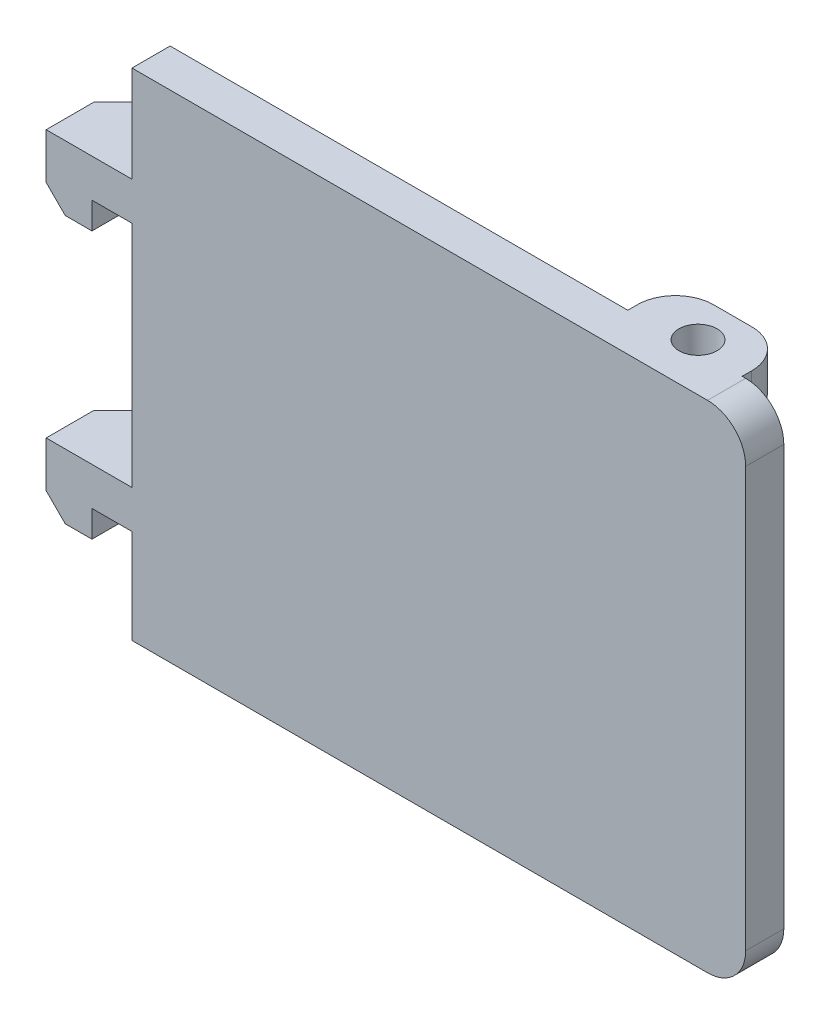
SolidWorks part; units mm, degrees
ref_plane "前视基准面" through (0, 0, 0) normal (0, 0, 1) x (1, 0, 0)
ref_plane "上视基准面" through (0, 0, 0) normal (0, 1, 0) x (1, 0, 0)
ref_plane "右视基准面" through (0, 0, 0) normal (1, 0, 0) x (0, 0, -1)
other "Configuration Table"
sketch "草图2" plane through (0, 0, 0) normal (0, 0, 1) x (1, 0, 0)
  line L1 (15.1907, -6.4342) -> (-16.9928, -6.4342)
  line L2 (15.1907, -6.4342) -> (15.1907, -32.4342)
  line L3 (15.1907, -32.4342) -> (-16.9928, -32.4342)
  line L4 (-16.9928, -6.4342) -> (-16.9928, -32.4342)
  line L6 (13.1907, -6.4342) -> (-12.8093, -6.4342) construction
  dimension "D1" = 32.1835
  dimension "D2" = 26
extrude "凸台-拉伸1" add sketch "草图2" along normal blind 2
fillet "圆角1" radius 2 2 edges at (15.1907, -32.4342, 1) (15.1907, -6.4342, 1)
sketch "草图5" plane through (0, 0, 0) normal (0, 0, -1) x (-1, 0, 0)
  line L1 (-13.0072, -6.4342) -> (-7.0072, -6.4342)
  line L2 (-13.0072, -6.4342) -> (-13.0072, -8.4342)
  line L3 (-13.0072, -8.4342) -> (-7.0072, -8.4342)
  line L4 (-7.0072, -6.4342) -> (-7.0072, -8.4342)
  line L5 (16.9928, -32.4342) -> (-13.1907, -32.4342) construction
  line L6 (-13.0072, -32.4342) -> (-7.0072, -32.4342)
  line L7 (-13.0072, -32.4342) -> (-13.0072, -30.4342)
  line L8 (-13.0072, -30.4342) -> (-7.0072, -30.4342)
  line L9 (-7.0072, -32.4342) -> (-7.0072, -30.4342)
  line L11 (16.9928, -6.4342) -> (16.9928, -32.4342) construction
  line L12 (-13.1907, -6.4342) -> (16.9928, -6.4342) construction
  dimension "D1" = 2
  dimension "D2" = 24
  dimension "D3" = 6
extrude "凸台-拉伸2" add sketch "草图5" along normal blind 2.5
fillet "圆角2" radius 2 4 edges at (7.0072, -7.4342, -2.5) (13.0072, -7.4342, -2.5) (7.0072, -31.4342, -2.5) (13.0072, -31.4342, -2.5)
sketch "草图6" plane through (0, -32.4342, 0) normal (0, -1, 0) x (1, 0, 0)
  line L1 (17.1907, 2) -> (17.1907, -8) construction
  line L2 (-16.9928, 2) -> (13.1907, 2) construction
  circle A0 centre (10.1907, -0.5) radius 1
  dimension "D1" = 2
  dimension "D2" = 7
  dimension "D3" = 2.5
extrude "切除-拉伸3" cut sketch "草图6" against normal blind 4 draft 2
sketch "草图7" plane through (0, -6.4342, 0) normal (0, 1, 0) x (1, 0, 0)
  circle A0 centre (10.1907, 0.5) radius 1
  arc A1 (10.9751, 0) -> (9.4064, 0) centre (10.1907, 0.5) ccw construction
extrude "切除-拉伸4" cut sketch "草图7" against normal blind 4 draft 2
sketch "草图8" plane through (0, 0, 0) normal (0, 0, -1) x (-1, 0, 0)
  line L0 (16.9928, -6.4342) -> (16.9928, -32.4342) construction
  line L1 (16.9928, -11.4842) -> (21.4928, -11.4842)
  line L2 (16.9928, -11.4842) -> (16.9928, -13.4842)
  line L3 (16.9928, -13.4842) -> (21.4928, -13.4842)
  line L4 (21.4928, -11.4842) -> (21.4928, -13.4842)
  line L5 (16.9928, -32.4342) -> (-7.0072, -32.4342) construction
  line L6 (16.9928, -25.4842) -> (21.4928, -25.4842)
  line L7 (16.9928, -25.4842) -> (16.9928, -27.4842)
  line L8 (16.9928, -27.4842) -> (21.4928, -27.4842)
  line L9 (21.4928, -25.4842) -> (21.4928, -27.4842)
  dimension "D1" = 4.95
  dimension "D2" = 18.95
  dimension "D3" = 2
  dimension "D4" = 4.5
extrude "凸台-拉伸3" add sketch "草图8" against normal blind 2
sketch "草图10" plane through (0, 0, 0) normal (0, 0, -1) x (-1, 0, 0)
  line L1 (21.4928, -13.4842) -> (19.0928, -13.4842)
  line L2 (21.4928, -13.4842) -> (21.4928, -14.8842)
  line L3 (21.4928, -14.8842) -> (19.0928, -14.8842)
  line L4 (19.0928, -13.4842) -> (19.0928, -14.8842)
  line L5 (21.4928, -27.4842) -> (19.0928, -27.4842)
  line L6 (21.4928, -27.4842) -> (21.4928, -28.8842)
  line L7 (21.4928, -28.8842) -> (19.0928, -28.8842)
  line L8 (19.0928, -27.4842) -> (19.0928, -28.8842)
  dimension "D1" = 2.4
  dimension "D2" = 1.4
extrude "凸台-拉伸4" add sketch "草图10" against normal blind 2 separate body
sketch "草图11" plane through (0, 0, 0) normal (0, 0, -1) x (-1, 0, 0)
  line L0 (16.9928, -6.4342) -> (16.9928, -11.4842) construction
  line L1 (21.4928, -11.4842) -> (12.9928, -11.4842)
  line L2 (21.4928, -11.4842) -> (21.4928, -13.4842)
  line L3 (21.4928, -13.4842) -> (12.9928, -13.4842)
  line L4 (12.9928, -11.4842) -> (12.9928, -13.4842)
  line L5 (21.4928, -25.4842) -> (12.9928, -25.4842)
  line L6 (21.4928, -25.4842) -> (21.4928, -27.4842)
  line L7 (21.4928, -27.4842) -> (12.9928, -27.4842)
  line L8 (12.9928, -25.4842) -> (12.9928, -27.4842)
  dimension "D1" = 4
extrude "凸台-拉伸5" add sketch "草图11" along normal blind 2.5
chamfer "倒角1" distance 2 angle 45 4 edges at (-21.4928, -12.4842, -2.5) (-21.4928, -26.4842, -2.5) (-12.9928, -26.4842, -2.5) (-12.9928, -12.4842, -2.5)
chamfer "倒角2" distance 1 angle 45 2 edges at (-21.4928, -14.8842, 1) (-21.4928, -28.8842, 1)
